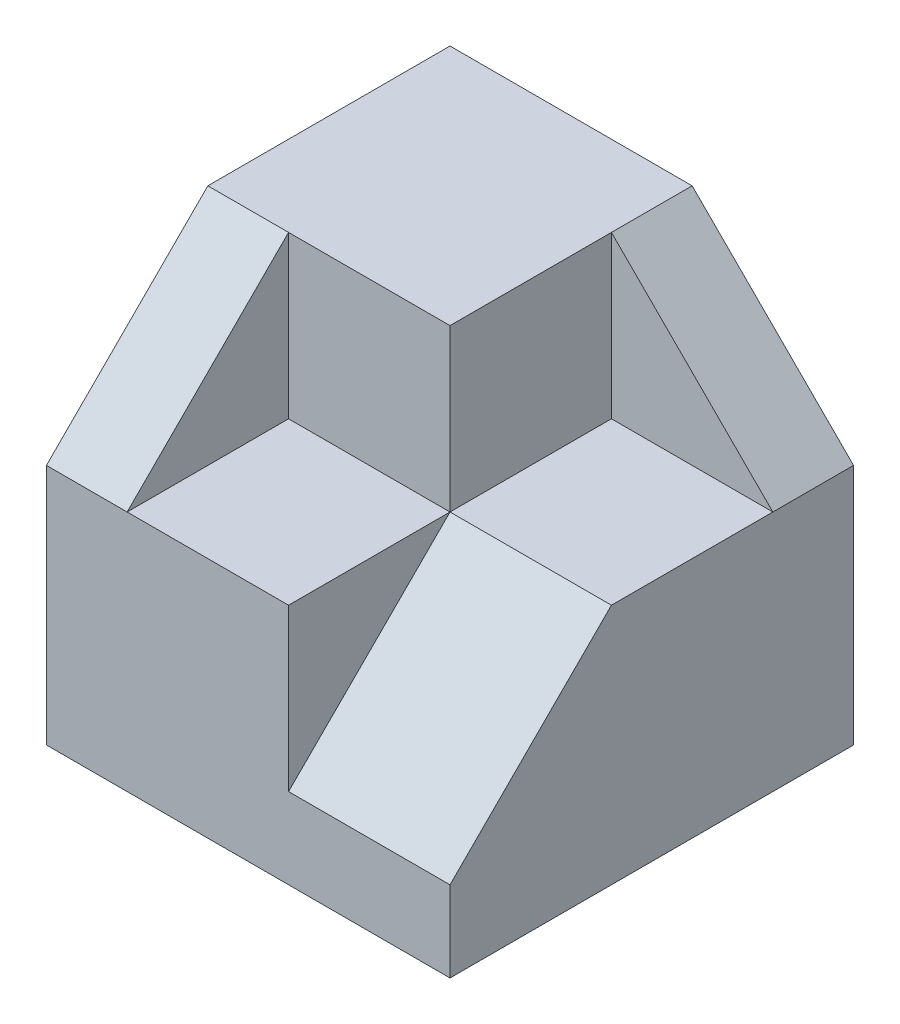
SolidWorks part; units mm, degrees
ref_plane "Front Plane" through (0, 0, 0) normal (0, 0, 1) x (1, 0, 0)
ref_plane "Top Plane" through (0, 0, 0) normal (0, 1, 0) x (1, 0, 0)
ref_plane "Right Plane" through (0, 0, 0) normal (1, 0, 0) x (0, 0, -1)
sketch "Sketch1" plane through (0, 0, 0) normal (0, 0, 1) x (1, 0, 0)
  line L1 (-2.5, -2.5) -> (2.5, -2.5)
  line L2 (-2.5, -2.5) -> (-2.5, 2.5)
  line L3 (-2.5, 2.5) -> (2.5, 2.5)
  line L4 (2.5, -2.5) -> (2.5, 2.5)
  line L5 (-2.5, -2.5) -> (2.5, 2.5) construction
  line L6 (-2.5, 2.5) -> (2.5, -2.5) construction
  point P0 (0, 0)
  dimension "D1" = 5
  dimension "D2" = 5
extrude "Boss-Extrude1" add sketch "Sketch1" along normal blind 5
sketch "Sketch2" plane through (0, 2.5, 0) normal (0, 1, 0) x (1, 0, 0)
  line L0 (2.5, -5) -> (-1.5, -5)
  line L1 (2.5, -5) -> (-2.5, -5) construction
  line L2 (-1.5, -5) -> (-1.5, -3)
  line L3 (-1.5, -3) -> (2.5, -3)
  line L4 (2.5, -5) -> (2.5, 0) construction
  line L5 (2.5, -3) -> (2.5, -5)
  dimension "D1" = 2
  dimension "D2" = 1
extrude "Cut-Extrude1" cut sketch "Sketch2" against normal blind 2
sketch "Sketch3" plane through (0, 2.5, 0) normal (0, 1, 0) x (1, 0, 0)
  line L0 (2.5, -1) -> (0.5, -1)
  line L1 (2.5, -3) -> (2.5, 0) construction
  line L2 (0.5, -1) -> (0.5, -3)
  line L3 (2.5, -3) -> (-1.5, -3) construction
  line L4 (0.5, -3) -> (2.5, -3)
  line L5 (2.5, -3) -> (-1.5, -3) construction
  line L6 (2.5, -3) -> (2.5, -1)
  dimension "D1" = 1
  dimension "D2" = 2
extrude "Cut-Extrude2" cut sketch "Sketch3" against normal blind 2
sketch "Sketch4" plane through (0, 0, 1) normal (0, 0, 1) x (1, 0, 0)
  line L0 (0.5, 2.5) -> (2.5, 0.5)
  line L1 (2.5, 0.5) -> (2.5, 2.5)
  line L2 (2.5, 2.5) -> (0.5, 2.5)
extrude "Cut-Extrude3" cut sketch "Sketch4" against normal through all
sketch "Sketch5" plane through (2.5, 0, 0) normal (1, 0, 0) x (0, 0, -1)
  line L0 (-5, 0.5) -> (-3, 0.5)
  line L2 (-5, -2.5) -> (-5, 0.5) construction
  line L3 (-5, -1.5) -> (-5, 0.5)
  line L4 (-5, 0.5) -> (-1, 0.5) construction
  line L5 (-3, 0.5) -> (-5, -1.5)
  dimension "D1" = 1
  dimension "D2" = 2
extrude "Cut-Extrude4" cut sketch "Sketch5" against normal blind 2
sketch "Sketch6" plane through (-1.5, 0, 0) normal (1, 0, 0) x (0, 0, -1)
  line L0 (-3, 2.5) -> (-5, 0.5)
  line L1 (-5, 0.5) -> (-5, 2.5)
  line L2 (-5, 2.5) -> (-3, 2.5)
extrude "Cut-Extrude5" cut sketch "Sketch6" against normal through all
